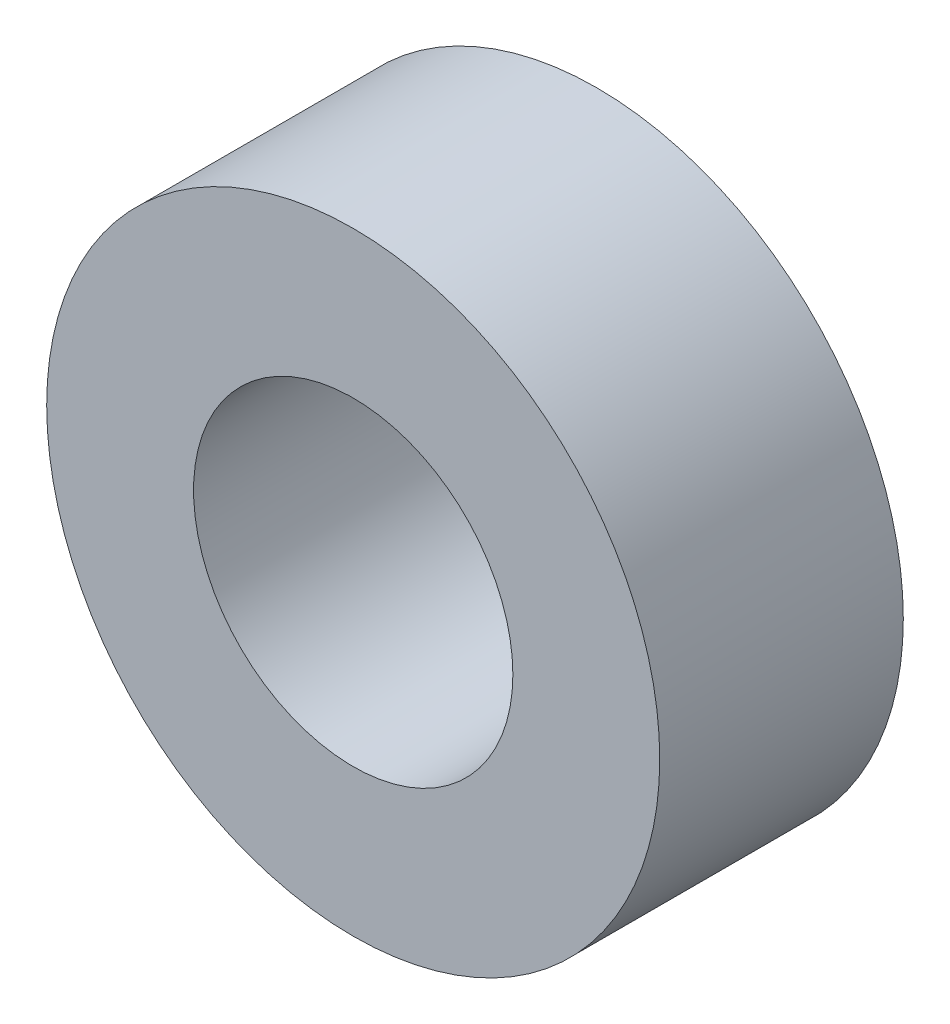
SolidWorks part; units mm, degrees
ref_plane "Front Plane" through (0, 0, 0) normal (0, 0, 1) x (1, 0, 0)
ref_plane "Top Plane" through (0, 0, 0) normal (0, 1, 0) x (1, 0, 0)
ref_plane "Right Plane" through (0, 0, 0) normal (1, 0, 0) x (0, 0, -1)
sketch "Sketch2" plane through (0, 0, 0) normal (0, 0, 1) x (1, 0, 0)
  circle A0 centre (0, 0) radius 1.25
  circle A1 centre (0, 0) radius 2.4
  dimension "D1" = 4.8
  dimension "D2" = 2.5
extrude "Boss-Extrude1" add sketch "Sketch2" along normal blind 1.907
